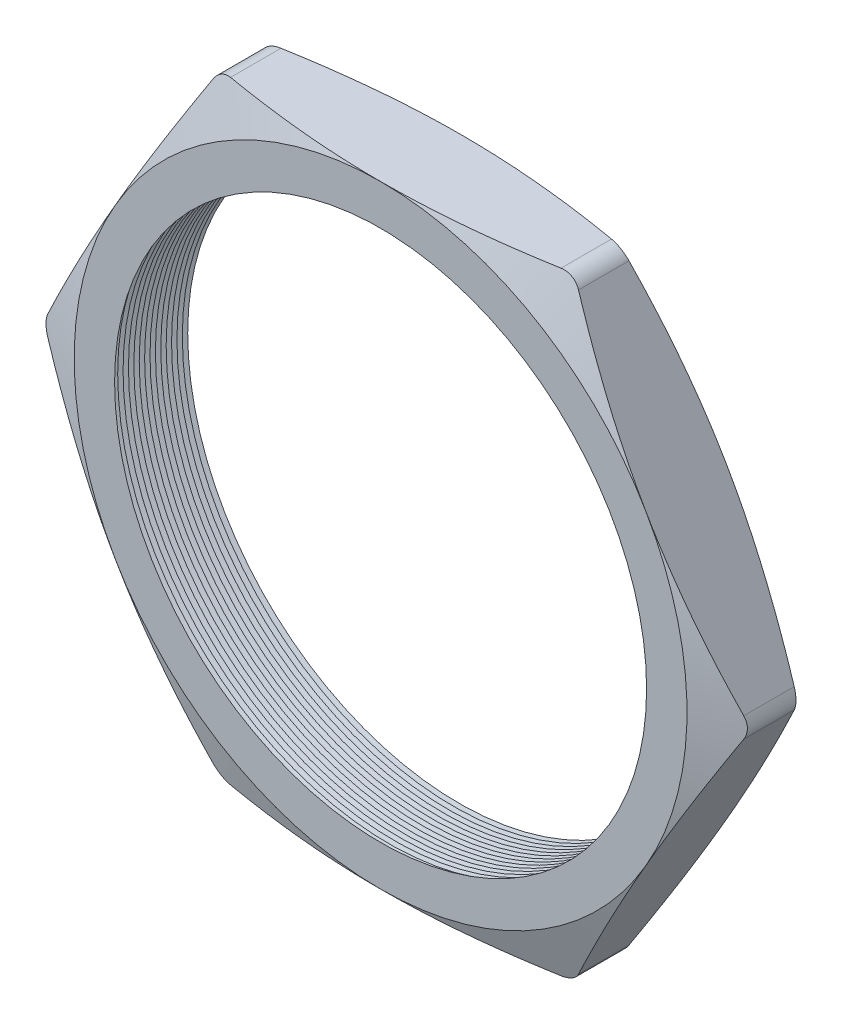
SolidWorks part; units mm, degrees
ref_plane "Front Plane" through (0, 0, 0) normal (0, 0, 1) x (1, 0, 0)
ref_plane "Top Plane" through (0, 0, 0) normal (0, 1, 0) x (1, 0, 0)
ref_plane "Right Plane" through (0, 0, 0) normal (1, 0, 0) x (0, 0, -1)
sketch "Sketch1" plane through (0, 0, 0) normal (0, 0, 1) x (1, 0, 0)
  line L1 (-13.3449, 0) -> (-6.6724, -11.557)
  line L2 (-6.6724, -11.557) -> (6.6724, -11.557)
  line L3 (6.6724, -11.557) -> (13.3449, 0)
  line L4 (13.3449, 0) -> (6.6724, 11.557)
  line L5 (6.6724, 11.557) -> (-6.6724, 11.557)
  line L6 (-6.6724, 11.557) -> (-13.3449, 0)
  circle A0 centre (0, 0) radius 11.557 construction
  circle A1 centre (0, 0) radius 10.033
  dimension "TS" = 20.066
  dimension "H" = 23.114
extrude "Extrude1" add sketch "Sketch1" along normal blind 3.048
fillet "Fillet1" radius 0.762 6 edges at (-6.6724, 11.557, 1.524) (-13.3449, 0, 1.524) (-6.6724, -11.557, 1.524) (6.6724, -11.557, 1.524) (13.3449, 0, 1.524) (6.6724, 11.557, 1.524)
sketch "Sketch2" plane through (0, 0, 3.048) normal (0, 0, 1) x (1, 0, 0)
  line L0 (6.2325, 11.557) -> (-6.2325, 11.557) construction
  circle A0 centre (0, 0) radius 11.557
extrude "Cut-Extrude1" cut sketch "Sketch2" against normal through all draft 70 flip side to cut
sketch "Sketch3" plane through (0, 0, 0) normal (0, 0, -1) x (-1, 0, 0)
  circle A0 centre (0, 0) radius 11.557
extrude "Cut-Extrude2" cut sketch "Sketch3" against normal through all draft 70 flip side to cut
sketch "Sketch4" plane through (0, 0, 0) normal (0, 1, 0) x (1, 0, 0)
  line L0 (-10.033, -3.048) -> (-10.033, -2.6081)
  line L2 (-10.033, -2.6081) -> (-10.414, -2.828)
  line L3 (-10.414, -2.828) -> (-10.033, -3.048)
  line L5 (-10.033, 0) -> (-10.033, -3.048) construction
  line L6 (-10.033, -3.048) -> (10.033, -3.048) construction
  dimension "D1" = 60
  dimension "D2" = 60
  dimension "D3" = 0.381
revolve "Cut-Revolve1" cut sketch "Sketch4" angle 360 about axis through (0, 0, 3.048) along (0, 0, -1)
pattern_linear "LPattern1" count 15 spacing 0.2032 along (0, 0, -1) of "Cut-Revolve1"
